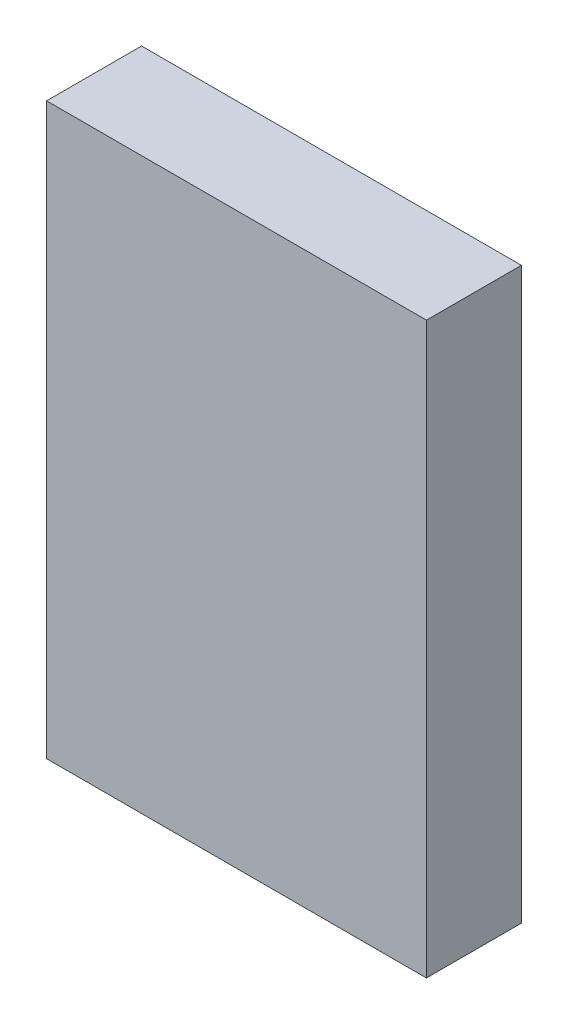
SolidWorks part; units mm, degrees
ref_plane "Front" through (0, 0, 0) normal (0, 0, 1) x (1, 0, 0)
ref_plane "Top" through (0, 0, 0) normal (0, 1, 0) x (1, 0, 0)
ref_plane "Right" through (0, 0, 0) normal (1, 0, 0) x (0, 0, -1)
sketch "Sketch1" plane through (0, 0, 0) normal (0, 0, 1) x (1, 0, 0)
  line L1 (0, 0) -> (20, 0)
  line L2 (0, 0) -> (0, 30)
  line L3 (0, 30) -> (20, 30)
  line L4 (20, 0) -> (20, 30)
  dimension "D1" = 20
  dimension "D2" = 30
extrude "Boss-Extrude1" add sketch "Sketch1" along normal blind 5
